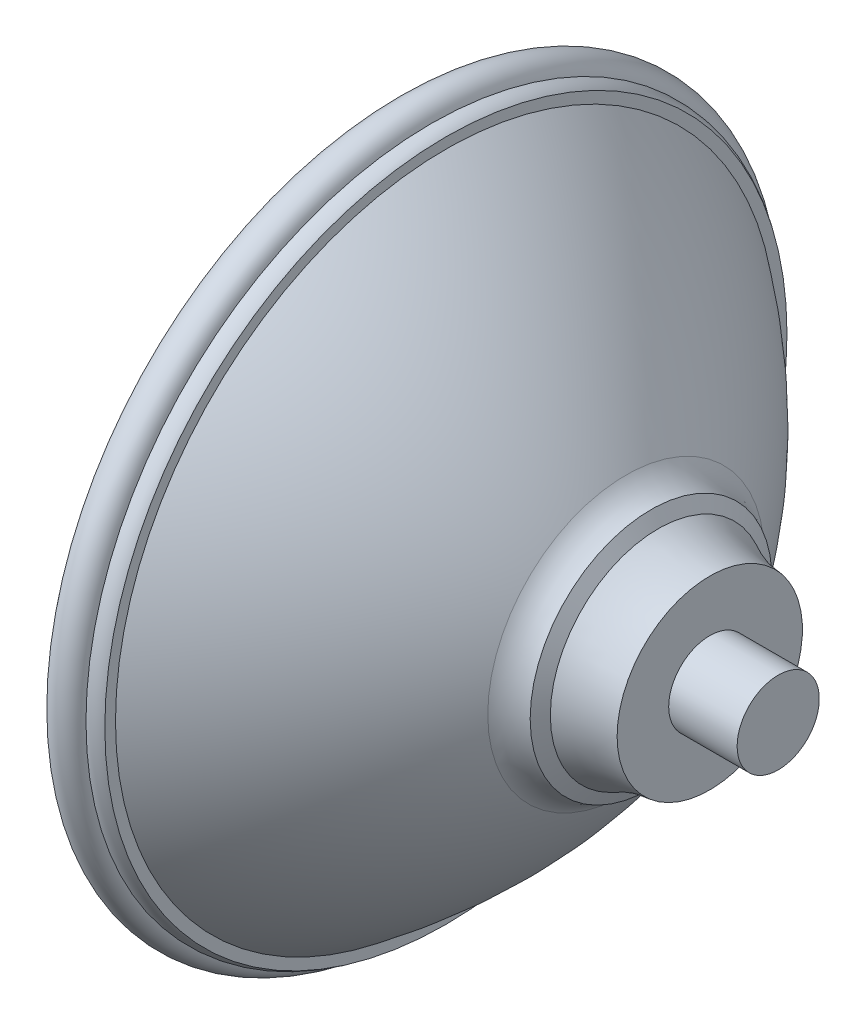
SolidWorks part; units mm, degrees
material "1060 Alloy"
ref_plane "Front Plane" through (0, 0, 0) normal (0, 0, 1) x (1, 0, 0)
ref_plane "Top Plane" through (0, 0, 0) normal (0, 1, 0) x (1, 0, 0)
ref_plane "Right Plane" through (0, 0, 0) normal (1, 0, 0) x (0, 0, -1)
sketch "Sketch2" plane through (0, 0, 0) normal (0, 0, 1) x (1, 0, 0)
  line L0 (0, 0) -> (0, 72.39) construction
  line L1 (0, 0) -> (0, -72.39) construction
  line L2 (-279.5787, 218.2506) -> (31.088, 218.2506) construction
  line L3 (-25.5974, 0) -> (0, 0)
  line L4 (0, 0) -> (73.977, 0)
  line L5 (73.977, 0) -> (73.977, 8.2998)
  line L6 (73.977, 8.2998) -> (60.1528, 8.2998)
  line L7 (60.1528, 8.2998) -> (60.1528, 18.718)
  line L8 (49.7367, 21.7908) -> (48.2948, 24.4247)
  line L9 (6.8489, 66.7446) -> (6.8489, 68.9006)
  arc A0 (-25.5974, 0) -> (-3.9595, 67.4033) centre (90.7303, -0.1689) cw
  arc A1 (60.1528, 18.718) -> (49.7367, 21.7908) centre (61.8989, 43.8275) cw
  arc A2 (-3.3286, 69.3131) -> (3.896, 69.7537) centre (0.3223, 68.9006) cw
  arc A3 (-3.3286, 69.3131) -> (-3.9595, 67.4033) centre (-17.4451, 72.9173) cw
  arc A4 (48.2948, 24.4247) -> (43.2313, 27.9272) centre (50.703, 33.3175) cw
  arc A5 (6.8489, 66.7446) -> (43.2313, 27.9272) centre (-79.6443, -50.7817) cw
  arc A6 (6.8489, 68.9006) -> (3.896, 69.7537) centre (4.3072, 65.6396) ccw
  dimension "D1" = 144.78
revolve "Revolve1" add sketch "Sketch2" angle 360 about L4
